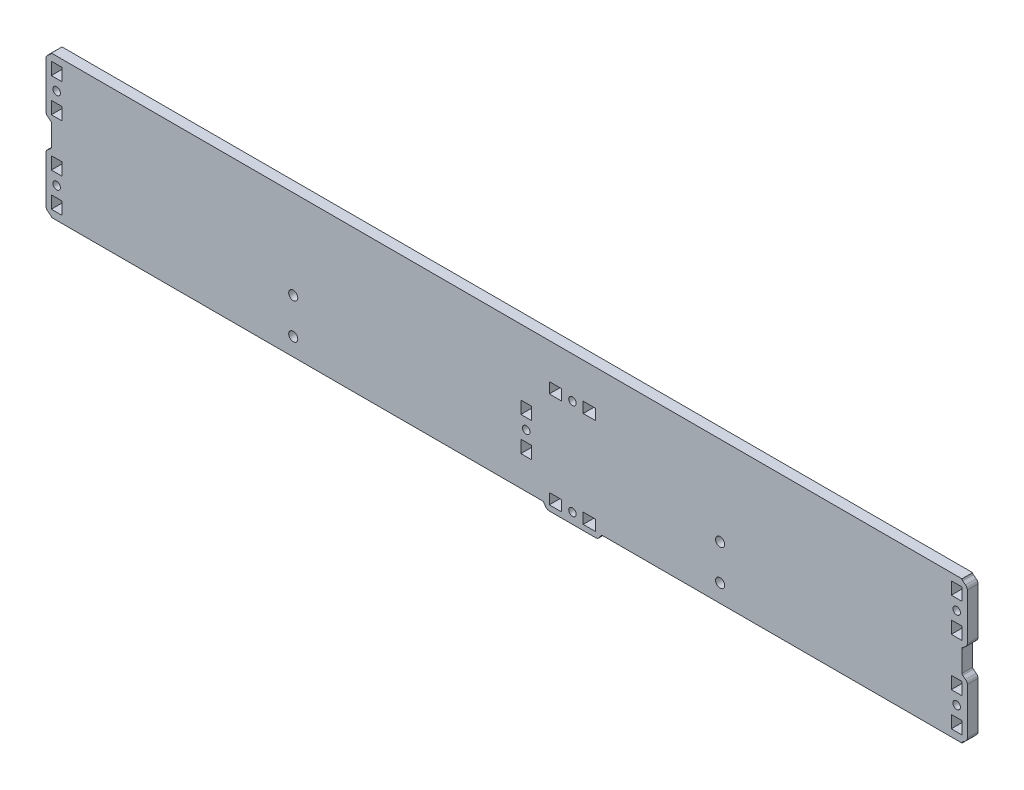
SolidWorks part; units mm, degrees
material "Клен"
ref_plane "Спереди" through (0, 0, 0) normal (0, 0, 1) x (1, 0, 0)
ref_plane "Сверху" through (0, 0, 0) normal (0, 1, 0) x (1, 0, 0)
ref_plane "Справа" through (0, 0, 0) normal (1, 0, 0) x (0, 0, -1)
sketch "Эскиз1" plane through (0, 0, 0) normal (0, 0, 1) x (1, 0, 0)
  line L0 (0, -164.4615) -> (512, -244.4615) construction
  line L1 (0, -244.4615) -> (512, -244.4615)
  line L2 (0, -244.4615) -> (0, -164.4615)
  line L3 (0, -164.4615) -> (512, -164.4615)
  line L4 (512, -244.4615) -> (512, -164.4615)
  line L5 (512, -164.4615) -> (0, -244.4615) construction
  line L6 (256, -229.8055) -> (256, -159.0937) construction
extrude "Бобышка-Вытянуть1" add sketch "Эскиз1" along normal blind 6 contours L3 L4 L1 L2
sketch "Эскиз2" plane through (0, 0, 6) normal (0, 0, 1) x (1, 0, 0)
  line L0 (0, -244.4615) -> (512, -164.4615) construction
  line L1 (512, -164.4615) -> (512, -244.4615) construction
  line L2 (512, -244.4615) -> (0, -164.4615) construction
  line L4 (256, -159.5243) -> (256, -268.7219) construction
  line L8 (0, -244.4615) -> (0, -164.4615) construction
  line L12 (0, -204.4615) -> (512, -204.4615) construction
  circle A4 centre (376, -234.4615) radius 2.55
  circle A5 centre (376, -214.4615) radius 2.55
  circle A6 centre (136, -234.4615) radius 2.55
  circle A7 centre (136, -214.4615) radius 2.55
  point P14 (0, -204.4615)
  point P16 (512, -204.4615)
  point P22 (256, -204.4615)
extrude "Вырез-Вытянуть1" cut sketch "Эскиз2" against normal through all
sketch "Эскиз21" plane through (462, -227.4615, 0) normal (0, 0, 1) x (0, -1, 0)
  line L0 (-13, 53) -> (13, 53)
  line L2 (15, 52) -> (16.2, 50.4)
  line L4 (17, 50) -> (-17, 50)
  line L5 (-15, 52) -> (-16.2, 50.4)
  arc A6 (13, 53) -> (15, 52) centre (13, 50.5) cw
  arc A7 (16.2, 50.4) -> (17, 50) centre (17, 51) ccw
  arc A8 (-13, 53) -> (-15, 52) centre (-13, 50.5) ccw
  arc A9 (-16.2, 50.4) -> (-17, 50) centre (-17, 51) cw
  point P12 (0, 53)
  point P13 (14.118, 52.7361)
  point P15 (-14.118, 52.7361)
  point P17 (0, 50)
  point P21 (14.118, 52.7361)
  dimension "D4" = 2.5
  dimension "D5" = 1
extrude "Бобышка-Вытянуть2" add sketch "Эскиз21" along normal blind 6
sketch "Эскиз3" plane through (462, -227.4615, 6) normal (0, 0, 1) x (0, -1, 0)
  line L1 (13.0318, 50) -> (6.0318, 50)
  line L2 (13.0318, 50) -> (13.0318, 44)
  line L3 (13.0318, 44) -> (6.0318, 44)
  line L4 (6.0318, 50) -> (6.0318, 44)
  line L5 (-13.0318, 44) -> (-6.0318, 44)
  line L6 (-13.0318, 50) -> (-13.0318, 44)
  line L7 (-6.0318, 50) -> (-6.0318, 44)
  line L8 (-13.0318, 50) -> (-6.0318, 50)
  circle A0 centre (0, 47) radius 2.1
  dimension "D1" = 4.2
extrude "Вырез-Вытянуть11" cut sketch "Эскиз3" against normal through all
other "Авто-элемент1<DIN967-9>"
sketch "Эскиз22" plane through (462, -181.4615, 0) normal (0, 0, 1) x (0, -1, 0)
  line L0 (-13, 53) -> (13, 53)
  line L2 (15, 52) -> (16.2, 50.4)
  line L4 (17, 50) -> (-17, 50)
  line L5 (-15, 52) -> (-16.2, 50.4)
  arc A6 (13, 53) -> (15, 52) centre (13, 50.5) cw
  arc A7 (16.2, 50.4) -> (17, 50) centre (17, 51) ccw
  arc A8 (-13, 53) -> (-15, 52) centre (-13, 50.5) ccw
  arc A9 (-16.2, 50.4) -> (-17, 50) centre (-17, 51) cw
  point P12 (0, 53)
  point P13 (14.118, 52.7361)
  point P15 (-14.118, 52.7361)
  point P17 (0, 50)
  point P21 (14.118, 52.7361)
  dimension "D4" = 2.5
  dimension "D5" = 1
extrude "Бобышка-Вытянуть21" add sketch "Эскиз22" along normal blind 6
sketch "Эскиз31" plane through (462, -181.4615, 6) normal (0, 0, 1) x (0, -1, 0)
  line L1 (13.0318, 50) -> (6.0318, 50)
  line L2 (13.0318, 50) -> (13.0318, 44)
  line L3 (13.0318, 44) -> (6.0318, 44)
  line L4 (6.0318, 50) -> (6.0318, 44)
  line L5 (-13.0318, 44) -> (-6.0318, 44)
  line L6 (-13.0318, 50) -> (-13.0318, 44)
  line L7 (-6.0318, 50) -> (-6.0318, 44)
  line L8 (-13.0318, 50) -> (-6.0318, 50)
  circle A0 centre (0, 47) radius 2.1
  dimension "D1" = 4.2
extrude "Вырез-Вытянуть12" cut sketch "Эскиз31" against normal through all
other "Авто-элемент2<DIN967-10>"
sketch "Эскиз23" plane through (50, -227.4615, 0) normal (0, 0, 1) x (0, 1, 0)
  line L0 (-13, 53) -> (13, 53)
  line L2 (15, 52) -> (16.2, 50.4)
  line L4 (17, 50) -> (-17, 50)
  line L5 (-15, 52) -> (-16.2, 50.4)
  arc A6 (13, 53) -> (15, 52) centre (13, 50.5) cw
  arc A7 (16.2, 50.4) -> (17, 50) centre (17, 51) ccw
  arc A8 (-13, 53) -> (-15, 52) centre (-13, 50.5) ccw
  arc A9 (-16.2, 50.4) -> (-17, 50) centre (-17, 51) cw
  point P12 (0, 53)
  point P13 (14.118, 52.7361)
  point P15 (-14.118, 52.7361)
  point P17 (0, 50)
  point P21 (14.118, 52.7361)
  dimension "D4" = 2.5
  dimension "D5" = 1
extrude "Бобышка-Вытянуть22" add sketch "Эскиз23" along normal blind 6
sketch "Эскиз32" plane through (50, -227.4615, 6) normal (0, 0, 1) x (0, 1, 0)
  line L1 (13.0318, 50) -> (6.0318, 50)
  line L2 (13.0318, 50) -> (13.0318, 44)
  line L3 (13.0318, 44) -> (6.0318, 44)
  line L4 (6.0318, 50) -> (6.0318, 44)
  line L5 (-13.0318, 44) -> (-6.0318, 44)
  line L6 (-13.0318, 50) -> (-13.0318, 44)
  line L7 (-6.0318, 50) -> (-6.0318, 44)
  line L8 (-13.0318, 50) -> (-6.0318, 50)
  circle A0 centre (0, 47) radius 2.1
  dimension "D1" = 4.2
extrude "Вырез-Вытянуть13" cut sketch "Эскиз32" against normal through all
other "Авто-элемент3<DIN967-12>"
sketch "Эскиз24" plane through (50, -181.4615, 0) normal (0, 0, 1) x (0, 1, 0)
  line L0 (-13, 53) -> (13, 53)
  line L2 (15, 52) -> (16.2, 50.4)
  line L4 (17, 50) -> (-17, 50)
  line L5 (-15, 52) -> (-16.2, 50.4)
  arc A6 (13, 53) -> (15, 52) centre (13, 50.5) cw
  arc A7 (16.2, 50.4) -> (17, 50) centre (17, 51) ccw
  arc A8 (-13, 53) -> (-15, 52) centre (-13, 50.5) ccw
  arc A9 (-16.2, 50.4) -> (-17, 50) centre (-17, 51) cw
  point P12 (0, 53)
  point P13 (14.118, 52.7361)
  point P15 (-14.118, 52.7361)
  point P17 (0, 50)
  point P21 (14.118, 52.7361)
  dimension "D4" = 2.5
  dimension "D5" = 1
extrude "Бобышка-Вытянуть23" add sketch "Эскиз24" along normal blind 6
sketch "Эскиз33" plane through (50, -181.4615, 6) normal (0, 0, 1) x (0, 1, 0)
  line L1 (13.0318, 50) -> (6.0318, 50)
  line L2 (13.0318, 50) -> (13.0318, 44)
  line L3 (13.0318, 44) -> (6.0318, 44)
  line L4 (6.0318, 50) -> (6.0318, 44)
  line L5 (-13.0318, 44) -> (-6.0318, 44)
  line L6 (-13.0318, 50) -> (-13.0318, 44)
  line L7 (-6.0318, 50) -> (-6.0318, 44)
  line L8 (-13.0318, 50) -> (-6.0318, 50)
  circle A0 centre (0, 47) radius 2.1
  dimension "D1" = 4.2
extrude "Вырез-Вытянуть14" cut sketch "Эскиз33" against normal through all
other "Авто-элемент4<DIN967-11>"
sketch "Эскиз35" plane through (314, -214.4615, 6) normal (0, 0, 1) x (0, 1, 0)
  line L0 (0, -127.8936) -> (0, 87.5572) construction
  line L1 (13.0318, 50) -> (6.0318, 50)
  line L2 (13.0318, 50) -> (13.0318, 44)
  line L3 (13.0318, 44) -> (6.0318, 44)
  line L4 (6.0318, 50) -> (6.0318, 44)
  line L5 (-13.0318, 44) -> (-6.0318, 44)
  line L6 (-13.0318, 50) -> (-13.0318, 44)
  line L7 (-6.0318, 50) -> (-6.0318, 44)
  line L8 (-13.0318, 50) -> (-6.0318, 50)
  circle A0 centre (0, 47) radius 2.1
  dimension "D1" = 4.2
extrude "Вырез-Вытянуть16" cut sketch "Эскиз35" against normal through all
other "Авто-элемент1<DIN967-1>"
sketch "Эскиз25" plane through (293, -194.4615, 0) normal (0, 0, 1) x (-1, 0, 0)
  line L0 (-13, 53) -> (13, 53)
  line L1 (0, -102.8936) -> (0, 112.5572) construction
  line L2 (15, 52) -> (16.2, 50.4)
  line L4 (17, 50) -> (-17, 50)
  line L5 (-15, 52) -> (-16.2, 50.4)
  arc A6 (13, 53) -> (15, 52) centre (13, 50.5) cw
  arc A7 (16.2, 50.4) -> (17, 50) centre (17, 51) ccw
  arc A8 (-13, 53) -> (-15, 52) centre (-13, 50.5) ccw
  arc A9 (-16.2, 50.4) -> (-17, 50) centre (-17, 51) cw
  point P12 (0, 53)
  point P13 (14.118, 52.7361)
  point P15 (-14.118, 52.7361)
  point P17 (0, 50)
  point P21 (14.118, 52.7361)
  dimension "D1" = 17
  dimension "D4" = 2.5
  dimension "D5" = 1
  dimension "D2" = 13
extrude "Бобышка-Вытянуть25" add sketch "Эскиз25" along normal blind 6
sketch "Эскиз36" plane through (293, -194.4615, 6) normal (0, 0, 1) x (-1, 0, 0)
  line L0 (0, -127.8936) -> (0, 87.5572) construction
  line L1 (13.0318, 50) -> (6.0318, 50)
  line L2 (13.0318, 50) -> (13.0318, 44)
  line L3 (13.0318, 44) -> (6.0318, 44)
  line L4 (6.0318, 50) -> (6.0318, 44)
  line L5 (-13.0318, 44) -> (-6.0318, 44)
  line L6 (-13.0318, 50) -> (-13.0318, 44)
  line L7 (-6.0318, 50) -> (-6.0318, 44)
  line L8 (-13.0318, 50) -> (-6.0318, 50)
  circle A0 centre (0, 47) radius 2.1
  dimension "D1" = 4.2
extrude "Вырез-Вытянуть17" cut sketch "Эскиз36" against normal through all
other "Авто-элемент2<DIN967-2>"
sketch "Эскиз37" plane through (293, -234.4615, 6) normal (0, 0, 1) x (1, 0, 0)
  line L0 (0, -127.8936) -> (0, 87.5572) construction
  line L1 (13.0318, 50) -> (6.0318, 50)
  line L2 (13.0318, 50) -> (13.0318, 44)
  line L3 (13.0318, 44) -> (6.0318, 44)
  line L4 (6.0318, 50) -> (6.0318, 44)
  line L5 (-13.0318, 44) -> (-6.0318, 44)
  line L6 (-13.0318, 50) -> (-13.0318, 44)
  line L7 (-6.0318, 50) -> (-6.0318, 44)
  line L8 (-13.0318, 50) -> (-6.0318, 50)
  circle A0 centre (0, 47) radius 2.1
  dimension "D1" = 4.2
extrude "Вырез-Вытянуть18" cut sketch "Эскиз37" against normal through all
other "Авто-элемент3<DIN967-3>"
